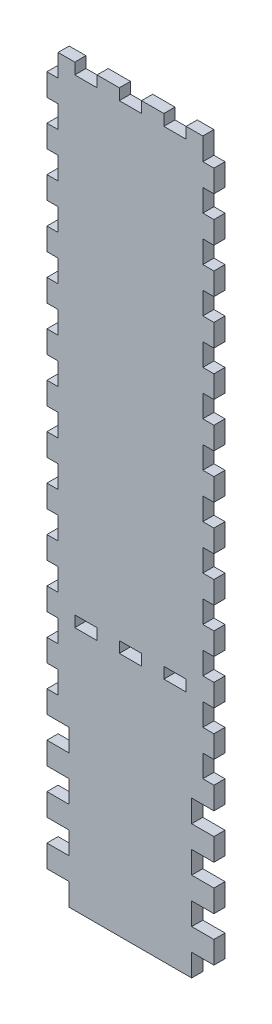
SolidWorks part; units mm, degrees
material "Pine"
ref_plane "Front Plane" through (0, 0, 0) normal (0, 0, 1) x (1, 0, 0)
ref_plane "Top Plane" through (0, 0, 0) normal (0, 1, 0) x (1, 0, 0)
ref_plane "Right Plane" through (0, 0, 0) normal (1, 0, 0) x (0, 0, -1)
sketch "Sketch2" plane through (0, 0, 0) normal (0, 0, 1) x (1, 0, 0)
  line L1 (0, 0) -> (95.25, 0)
  line L2 (0, 0) -> (0, 419.1)
  line L3 (0, 419.1) -> (95.25, 419.1)
  line L4 (95.25, 0) -> (95.25, 419.1)
  dimension "D1" = 95.25
  dimension "D2" = 419.1
extrude "Boss-Extrude1" add sketch "Sketch2" along normal blind 6.35
sketch "Sketch3" plane through (0, 0, 6.35) normal (0, 0, 1) x (1, 0, 0)
  line L1 (0, 0) -> (6.35, 0)
  line L2 (0, 0) -> (0, 12.7)
  line L3 (0, 12.7) -> (6.35, 12.7)
  line L4 (6.35, 0) -> (6.35, 12.7)
  line L5 (95.25, 0) -> (88.9, 0)
  line L6 (95.25, 0) -> (95.25, 12.7)
  line L7 (95.25, 12.7) -> (88.9, 12.7)
  line L8 (88.9, 0) -> (88.9, 12.7)
  dimension "D1" = 6.35
  dimension "D2" = 12.7
extrude "Cut-Extrude1" cut sketch "Sketch3" against normal through all
pattern_linear "LPattern1" count 17 spacing 25.4 along (0, 1, 0) of "Cut-Extrude1"
sketch "Sketch4" plane through (0, 0, 6.35) normal (0, 0, 1) x (1, 0, 0)
  line L0 (88.9, 419.1) -> (6.35, 419.1) construction
  line L1 (41.275, 419.1) -> (53.975, 419.1)
  line L2 (41.275, 419.1) -> (41.275, 412.75)
  line L3 (41.275, 412.75) -> (53.975, 412.75)
  line L4 (53.975, 419.1) -> (53.975, 412.75)
  line L5 (28.575, 419.1) -> (15.875, 419.1)
  line L6 (66.675, 419.1) -> (79.375, 419.1)
  line L7 (66.675, 419.1) -> (66.675, 412.75)
  line L8 (66.675, 412.75) -> (79.375, 412.75)
  line L9 (79.375, 419.1) -> (79.375, 412.75)
  line L10 (28.575, 419.1) -> (28.575, 412.75)
  line L11 (28.575, 412.75) -> (15.875, 412.75)
  line L12 (15.875, 419.1) -> (15.875, 412.75)
  point P14 (47.625, 419.1)
  dimension "D1" = 12.7
  dimension "D2" = 6.35
  dimension "D3" = 12.7
  dimension "D4" = 12.7
extrude "Cut-Extrude2" cut sketch "Sketch4" against normal through all
sketch "Sketch5" plane through (0, 0, 6.35) normal (0, 0, 1) x (1, 0, 0)
  line L0 (6.35, 0) -> (88.9, 0) construction
  line L1 (6.35, 12.7) -> (12.7, 12.7)
  line L2 (6.35, 12.7) -> (6.35, 0)
  line L3 (6.35, 0) -> (12.7, 0)
  line L4 (12.7, 12.7) -> (12.7, 0)
  line L5 (6.35, 12.7) -> (0, 12.7) construction
  line L6 (88.9, 12.7) -> (82.55, 12.7)
  line L7 (88.9, 12.7) -> (88.9, 0)
  line L8 (88.9, 0) -> (82.55, 0)
  line L9 (82.55, 12.7) -> (82.55, 0)
extrude "Cut-Extrude3" cut sketch "Sketch5" against normal through all
pattern_linear "LPattern2" count 4 spacing 25.4 along (0, 1, 0) of "Cut-Extrude3"
sketch "Sketch6" plane through (0, 0, 6.35) normal (0, 0, 1) x (1, 0, 0)
  line L0 (6.35, 139.7) -> (0, 139.7) construction
  line L1 (53.975, 139.7) -> (41.275, 139.7)
  line L2 (53.975, 139.7) -> (53.975, 146.05)
  line L3 (53.975, 146.05) -> (41.275, 146.05)
  line L4 (41.275, 139.7) -> (41.275, 146.05)
  line L5 (47.625, 139.7) -> (47.625, 0) construction
  line L6 (12.7, 0) -> (82.55, 0) construction
  dimension "D1" = 12.7
  dimension "D2" = 6.35
extrude "Cut-Extrude4" cut sketch "Sketch6" against normal through all
pattern_linear "LPattern3" count 2 spacing 25.4 along (1, 0, 0) count 2 spacing 25.4 along (-1, 0, 0) of "Cut-Extrude4"
